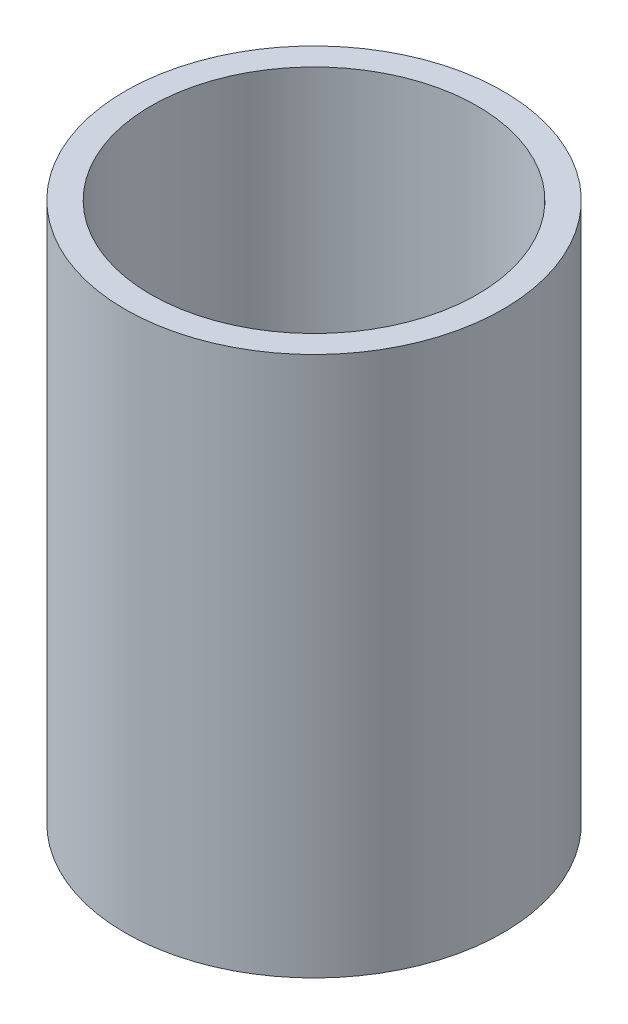
SolidWorks part; units mm, degrees
material "Corrugated Paper"
ref_plane "Front Plane" through (0, 0, 0) normal (0, 0, 1) x (1, 0, 0)
ref_plane "Top Plane" through (0, 0, 0) normal (0, 1, 0) x (1, 0, 0)
ref_plane "Right Plane" through (0, 0, 0) normal (1, 0, 0) x (0, 0, -1)
ref_axis "Axis1" through (0, 55, 0) along (0, -1, 0)
sketch "Sketch1" plane through (0, 0, 0) normal (0, 0, 1) x (1, 0, 0)
  line L1 (-46.6725, 45.6176) -> (-40.3225, 45.6176)
  line L2 (-46.6725, 45.6176) -> (-46.6725, -87.7324)
  line L3 (-46.6725, -87.7324) -> (-40.3225, -87.7324)
  line L4 (-40.3225, 45.6176) -> (-40.3225, -87.7324)
  line L5 (-38.1, 45.6176) -> (0, 45.6176) construction
  line L6 (-38.1, -87.7324) -> (0, -87.7324) construction
revolve "Revolve1" add sketch "Sketch1" angle 360 about axis through (0, 55, 0) along (0, -1, 0)
